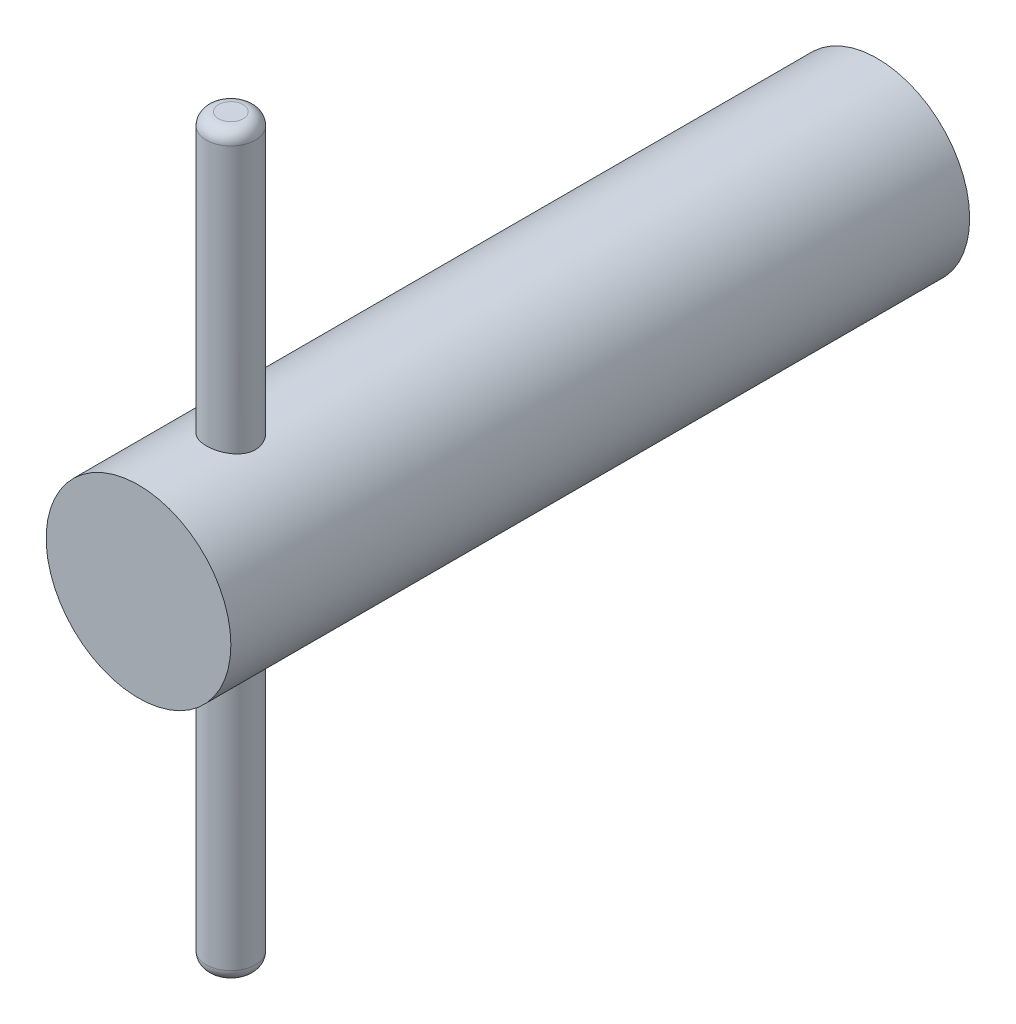
SolidWorks part; units mm, degrees
ref_plane "Alzado" through (0, 0, 0) normal (0, 0, 1) x (1, 0, 0)
ref_plane "Planta" through (0, 0, 0) normal (0, 1, 0) x (1, 0, 0)
ref_plane "Vista lateral" through (0, 0, 0) normal (1, 0, 0) x (0, 0, -1)
sketch "Croquis2" plane through (0, 0, 0) normal (0, 0, 1) x (1, 0, 0)
  circle A0 centre (0, 0) radius 15
  dimension "D1" = 30
extrude "Saliente-Extruir1" add sketch "Croquis2" along normal blind 120
sketch "Croquis3" plane through (0, 0, 0) normal (0, 0, -1) x (-1, 0, 0)
  line L1 (5.7417, 10.0183) -> (-5.8052, 9.9816)
  line L2 (-5.8052, 9.9816) -> (-11.5469, -0.0367)
  line L3 (-11.5469, -0.0367) -> (-5.7417, -10.0183)
  line L4 (-5.7417, -10.0183) -> (5.8052, -9.9816)
  line L5 (5.8052, -9.9816) -> (11.5469, 0.0367)
  line L6 (11.5469, 0.0367) -> (5.7417, 10.0183)
  circle A0 centre (0, 0) radius 10 construction
  dimension "D1" = 20
extrude "Cortar-Extruir1" cut sketch "Croquis3" against normal blind 50
sketch "Croquis4" plane through (0, 0, 0) normal (0, 1, 0) x (1, 0, 0)
  line L0 (-15, -120) -> (15, -120) construction
  circle A0 centre (0, -105) radius 4
  dimension "D1" = 8
  dimension "D2" = 15
extrude "Saliente-Extruir2" add sketch "Croquis4" along normal mid plane 120
fillet "Redondeo5" radius 2 2 edges at (0, 60, 109) (0, -60, 109)
